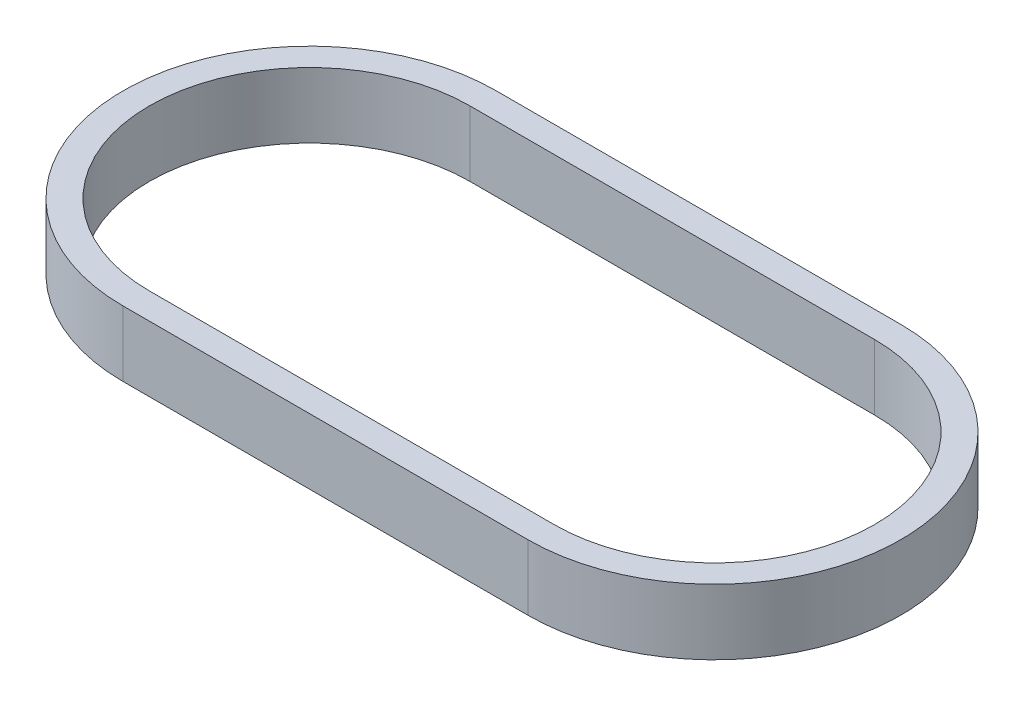
SolidWorks part; units mm, degrees
ref_plane "Front" through (0, 0, 0) normal (0, 0, 1) x (1, 0, 0)
ref_plane "Top" through (0, 0, 0) normal (0, 1, 0) x (1, 0, 0)
ref_plane "Right" through (0, 0, 0) normal (1, 0, 0) x (0, 0, -1)
sketch "Sketch1" plane through (0, 0, 0) normal (0, 1, 0) x (1, 0, 0)
  line L0 (0, 36.1721) -> (78.5207, 36.1721)
  line L1 (0, -36.1721) -> (78.5207, -36.1721)
  line L2 (0, 31.0921) -> (78.5207, 31.0921)
  line L3 (0, -31.0921) -> (78.5207, -31.0921)
  arc A0 (0, 36.1721) -> (0, -36.1721) centre (0, 0) ccw
  arc A1 (78.5207, -36.1721) -> (78.5207, 36.1721) centre (78.5207, 0) ccw
  arc A2 (78.5207, -31.0921) -> (78.5207, 31.0921) centre (78.5207, 0) ccw
  arc A3 (0, 31.0921) -> (0, -31.0921) centre (0, 0) ccw
  circle A5 centre (78.5207, 0) radius 36.1718 construction
  dimension "D1" = 72.3443
  dimension "D2" = 5.08
extrude "Boss-Extrude1" add sketch "Sketch1" along normal blind 12.7
